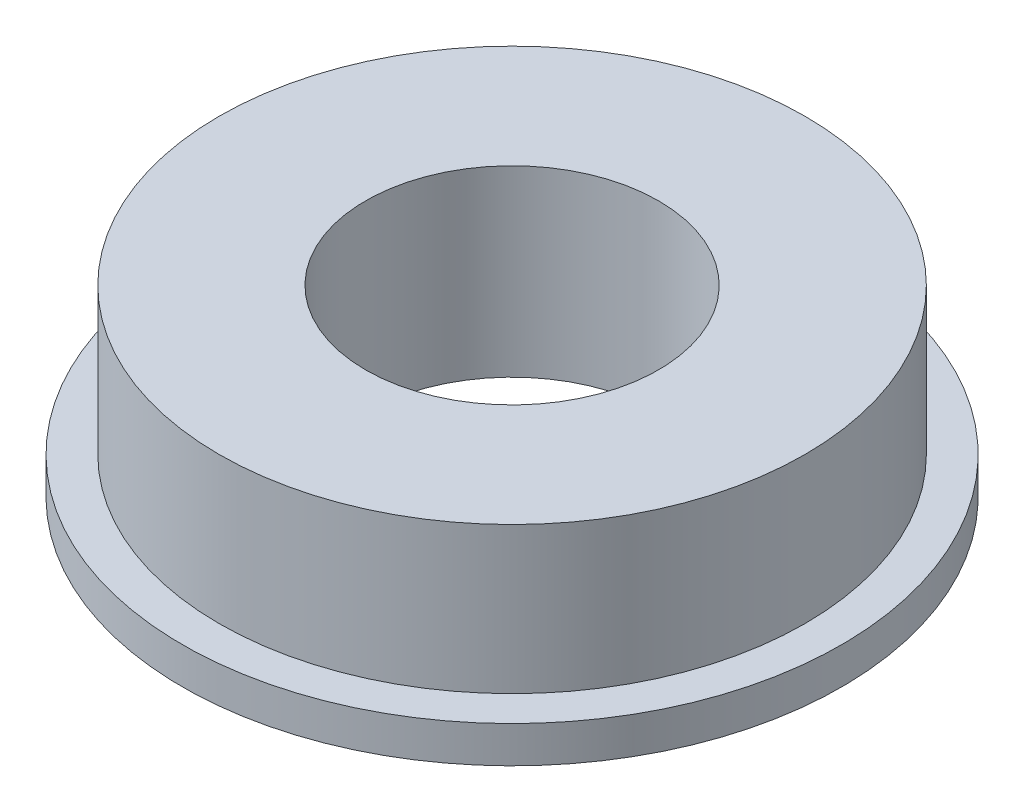
SolidWorks part; units mm, degrees
ref_plane "Front Plane" through (0, 0, 0) normal (0, 0, 1) x (1, 0, 0)
ref_plane "Top Plane" through (0, 0, 0) normal (0, 1, 0) x (1, 0, 0)
ref_plane "Right Plane" through (0, 0, 0) normal (1, 0, 0) x (0, 0, -1)
sketch "Sketch1" plane through (0, 0, 0) normal (0, 0, 1) x (1, 0, 0)
  line L0 (-4, -2.5) -> (-4, 2.5)
  line L1 (-4, 2.5) -> (-8, 2.5)
  line L2 (-8, 2.5) -> (-8, -1.5)
  line L3 (-8, -1.5) -> (-9, -1.5)
  line L4 (-9, -1.5) -> (-9, -2.5)
  line L5 (-9, -2.5) -> (-4, -2.5)
  line L6 (0, -2.5) -> (0, 2.5)
  dimension "D1" = 5
  dimension "D2" = 1
  dimension "D3" = 1
  dimension "D4" = 5
  dimension "D5" = 4
revolve "Revolve1" add sketch "Sketch1" angle 360 about L6
